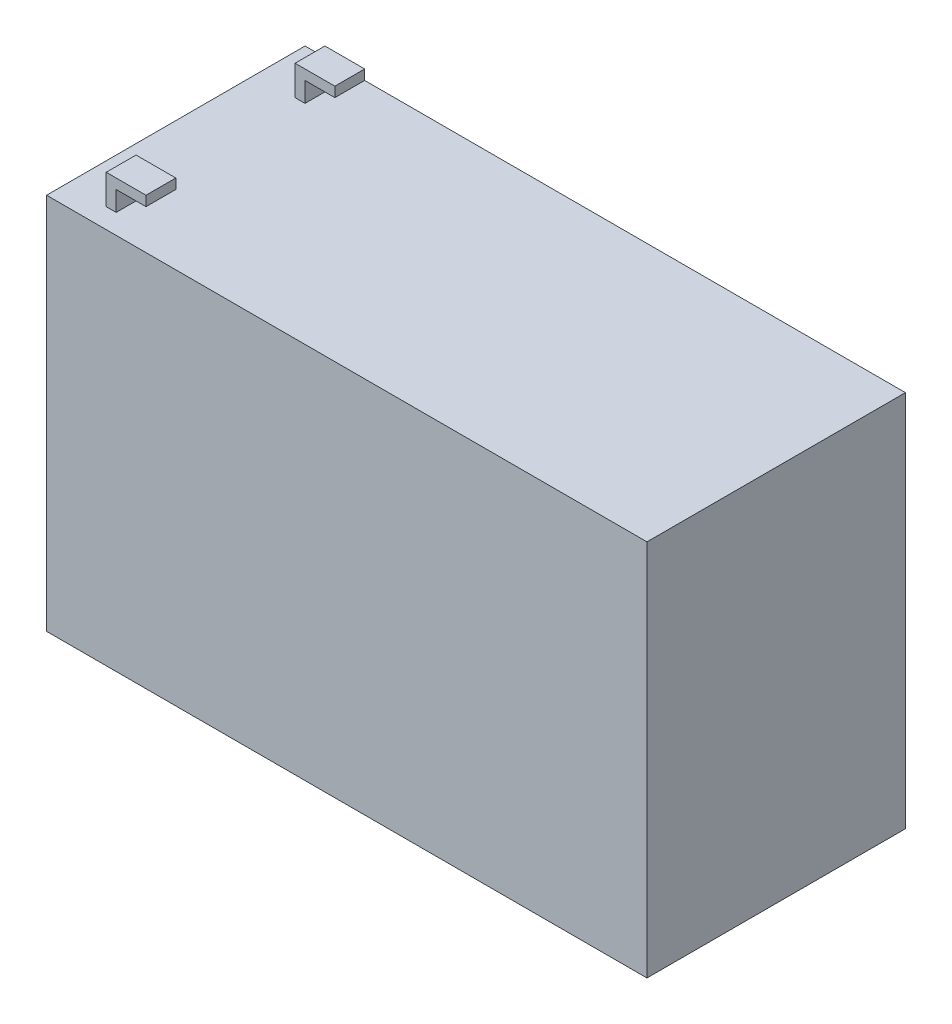
SolidWorks part; units mm, degrees
ref_plane "Front Plane" through (0, 0, 0) normal (0, 0, 1) x (1, 0, 0)
ref_plane "Top Plane" through (0, 0, 0) normal (0, 1, 0) x (1, 0, 0)
ref_plane "Right Plane" through (0, 0, 0) normal (1, 0, 0) x (0, 0, -1)
sketch "Sketch1" plane through (0, 0, 0) normal (0, 0, 1) x (1, 0, 0)
  line L1 (-75.5, 47.5) -> (75.5, 47.5)
  line L2 (-75.5, 47.5) -> (-75.5, -47.5)
  line L3 (-75.5, -47.5) -> (75.5, -47.5)
  line L4 (75.5, 47.5) -> (75.5, -47.5)
  point P4 (-75.5, 0)
  point P5 (0, 47.5)
  dimension "D1" = 151
  dimension "D2" = 95
extrude "Boss-Extrude1" add sketch "Sketch1" against normal blind 65
sketch "Sketch2" plane through (0, 0, 0) normal (0, 0, 1) x (1, 0, 0)
  line L0 (-65.5, 47.5) -> (-65.5, 55)
  line L1 (-65.5, 55) -> (-55.5, 55)
  line L2 (-55.5, 55) -> (-55.5, 52.5)
  line L3 (-55.5, 52.5) -> (-63, 52.5)
  line L4 (-63, 52.5) -> (-63, 47.5)
  line L5 (-63, 47.5) -> (-65.5, 47.5)
  line L6 (75.5, 47.5) -> (-75.5, 47.5) construction
  line L7 (-75.5, 47.5) -> (-75.5, -47.5) construction
  dimension "D1" = 2.5
  dimension "D2" = 7.5
  dimension "2.5" = 2.5
  dimension "D3" = 10
  dimension "D4" = 10
extrude "Boss-Extrude2" add sketch "Sketch2" against normal blind 65
sketch "Sketch3" plane through (-65.5, 0, 0) normal (-1, 0, 0) x (0, 0, 1)
  line L0 (-65, 47.5) -> (0, 47.5) construction
  line L1 (-65, 55) -> (-65, 47.5) construction
  line L2 (-60, 47.5) -> (-65, 47.5)
  line L3 (-60, 47.5) -> (-60, 55)
  line L4 (-60, 55) -> (-65, 55)
  line L5 (-65, 47.5) -> (-65, 55)
  line L6 (-52.5, 55) -> (-12.5, 55)
  line L7 (-52.5, 55) -> (-52.5, 47.5)
  line L8 (-52.5, 47.5) -> (-12.5, 47.5)
  line L9 (-12.5, 55) -> (-12.5, 47.5)
  line L10 (-65, 55) -> (0, 55) construction
  line L11 (-65, 47.5) -> (0, 47.5) construction
  line L12 (-5, 55) -> (0, 55)
  line L13 (-5, 55) -> (-5, 47.5)
  line L14 (-5, 47.5) -> (0, 47.5)
  line L15 (0, 55) -> (0, 47.5)
  line L16 (0, 55) -> (0, 47.5) construction
  dimension "D1" = 5
  dimension "D2" = 7.5
  dimension "7.5" = 7.5
  dimension "D3" = 5
extrude "Cut-Extrude1" cut sketch "Sketch3" against normal up to next
